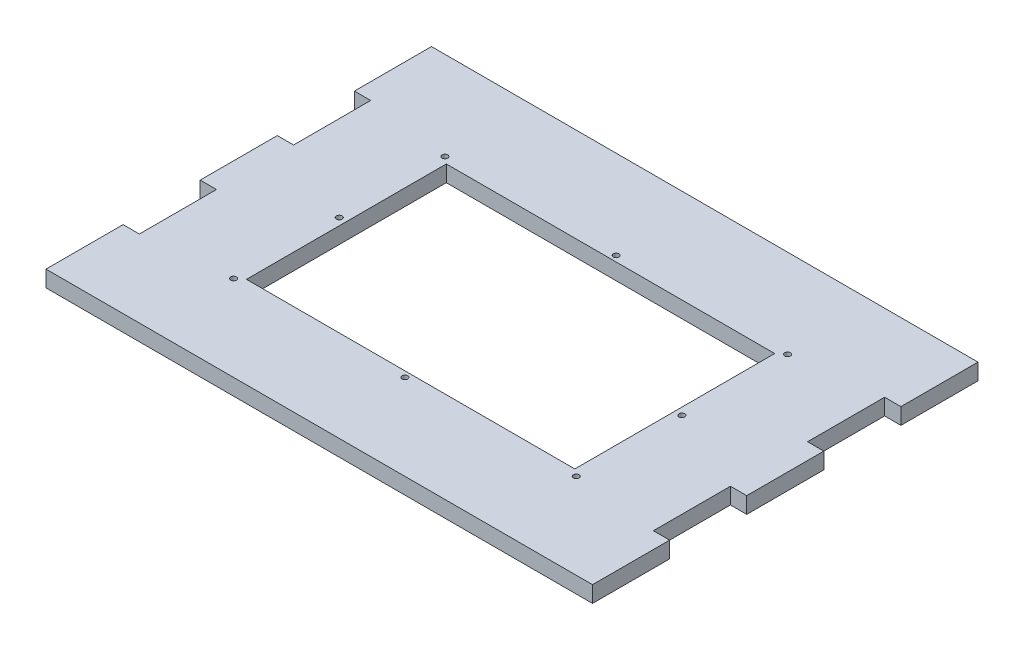
SolidWorks part; units mm, degrees
ref_plane "Front Plane" through (0, 0, 0) normal (0, 0, 1) x (1, 0, 0)
ref_plane "Top Plane" through (0, 0, 0) normal (0, 1, 0) x (1, 0, 0)
ref_plane "Right Plane" through (0, 0, 0) normal (1, 0, 0) x (0, 0, -1)
sketch "Sketch1" plane through (0, 0, 0) normal (0, 1, 0) x (1, 0, 0)
  line L0 (0, 0) -> (180, 0)
  line L1 (0, 100) -> (180, 100)
  line L2 (0, 0) -> (0, 100)
  line L4 (180, 0) -> (180, 100)
sketch "Sketch2" plane through (0, 0, 0) normal (0, 1, 0) x (1, 0, 0)
  line L1 (0, -6) -> (180, -6)
  line L2 (0, -6) -> (0, 106)
  line L3 (0, 106) -> (180, 106)
  line L4 (180, -6) -> (180, 106)
sketch "Sketch3" plane through (0, 0, 0) normal (0, 1, 0) x (1, 0, 0)
  line L1 (-6, -14) -> (186, -14)
  line L2 (-6, -14) -> (-6, 121)
  line L3 (-6, 121) -> (186, 121)
  line L4 (186, -14) -> (186, 121)
extrude "Boss-Extrude1" add sketch "Sketch3" along normal blind 5.7
ref_plane "Plane1" through (0, 5.7, 0) normal (0, 1, 0) x (1, 0, 0)
sketch "Sketch5" plane through (0, 5.7, 0) normal (0, 1, 0) x (1, 0, 0)
  line L0 (0, 0) -> (180, 0)
  line L1 (0, 100) -> (180, 100)
  line L2 (0, 0) -> (0, 100)
  line L4 (180, 0) -> (180, 100)
sketch "Sketch7" plane through (0, 5.7, 0) normal (0, 1, 0) x (1, 0, 0)
  line L1 (0, -6) -> (180, -6)
  line L2 (0, -6) -> (0, 106)
  line L3 (0, 106) -> (180, 106)
  line L4 (180, -6) -> (180, 106)
sketch "Sketch8" plane through (0, 0, 0) normal (0, 1, 0) x (1, 0, 0)
  line L4 (35, 23) -> (145, 23)
  line L5 (35, 23) -> (35, 83)
  line L6 (35, 83) -> (145, 83)
  line L7 (145, 23) -> (145, 83)
  line L8 (35, 23) -> (145, 83) construction
  line L9 (35, 83) -> (145, 23) construction
  point P6 (90, 53)
  point P7 (90, 53)
sketch "Sketch9" plane through (0, 0, 0) normal (0, 1, 0) x (1, 0, 0)
  line L1 (32.5, 88) -> (147.5, 88)
  line L2 (32.5, 88) -> (32.5, 18)
  line L3 (32.5, 18) -> (147.5, 18)
  line L4 (147.5, 88) -> (147.5, 18)
  line L5 (32.5, 88) -> (147.5, 18) construction
  line L6 (32.5, 18) -> (147.5, 88) construction
  point P0 (90, 53)
sketch "Sketch10" plane through (0, 0, 0) normal (0, 1, 0) x (1, 0, 0)
  line L1 (27, 93) -> (153, 93)
  line L2 (27, 93) -> (27, 13)
  line L3 (27, 13) -> (153, 13)
  line L4 (153, 93) -> (153, 13)
  line L5 (27, 93) -> (153, 13) construction
  line L6 (27, 13) -> (153, 93) construction
  point P0 (90, 53)
extrude "Cut-Extrude2" cut sketch "Sketch9" along normal blind 47
sketch "Sketch12" plane through (0, 0, 0) normal (0, 1, 0) x (1, 0, 0)
  line L1 (30, 90) -> (150, 90) construction
  line L2 (30, 90) -> (30, 16) construction
  line L3 (30, 16) -> (150, 16) construction
  line L4 (150, 90) -> (150, 16) construction
  line L5 (30, 90) -> (150, 16) construction
  line L6 (30, 16) -> (150, 90) construction
  circle A0 centre (30, 90) radius 1
  circle A1 centre (30, 53) radius 1
  circle A2 centre (30, 16) radius 1
  circle A3 centre (90, 16) radius 1
  circle A4 centre (150, 16) radius 1
  circle A5 centre (150, 53) radius 1
  circle A6 centre (150, 90) radius 1
  circle A7 centre (90, 90) radius 1
  point P0 (90, 53)
extrude "Cut-Extrude3" cut sketch "Sketch12" along normal blind 37
sketch "Sketch13" plane through (0, 0, 0) normal (0, 1, 0) x (1, 0, 0)
  line L0 (-5.7, 121) -> (-5.7, 94)
  line L2 (-5.7, 94) -> (0, 94)
  line L4 (0, 94) -> (0, 67)
  line L5 (0, 67) -> (-5.7, 67)
  line L6 (-5.7, 67) -> (-5.7, 40)
  line L7 (-5.7, 40) -> (0, 40)
  line L8 (0, 40) -> (0, 13)
  line L9 (0, 13) -> (-5.7, 13)
  line L10 (-5.7, 13) -> (-5.7, -14)
  line L11 (-5.7, -14) -> (-9.7, -14)
  line L12 (-9.7, -14) -> (-9.7, 121)
  line L13 (-9.7, 121) -> (-5.7, 121)
  line L14 (90, 131) -> (90, -20) construction
  line L15 (189.7, 121) -> (185.7, 121)
  line L16 (189.7, -14) -> (189.7, 121)
  line L17 (185.7, -14) -> (189.7, -14)
  line L18 (185.7, 13) -> (185.7, -14)
  line L19 (180, 13) -> (185.7, 13)
  line L20 (180, 40) -> (180, 13)
  line L21 (185.7, 40) -> (180, 40)
  line L22 (185.7, 67) -> (185.7, 40)
  line L23 (180, 67) -> (185.7, 67)
  line L24 (180, 94) -> (180, 67)
  line L25 (185.7, 94) -> (180, 94)
  line L26 (185.7, 121) -> (185.7, 94)
extrude "Cut-Extrude4" cut sketch "Sketch13" along normal blind 11
